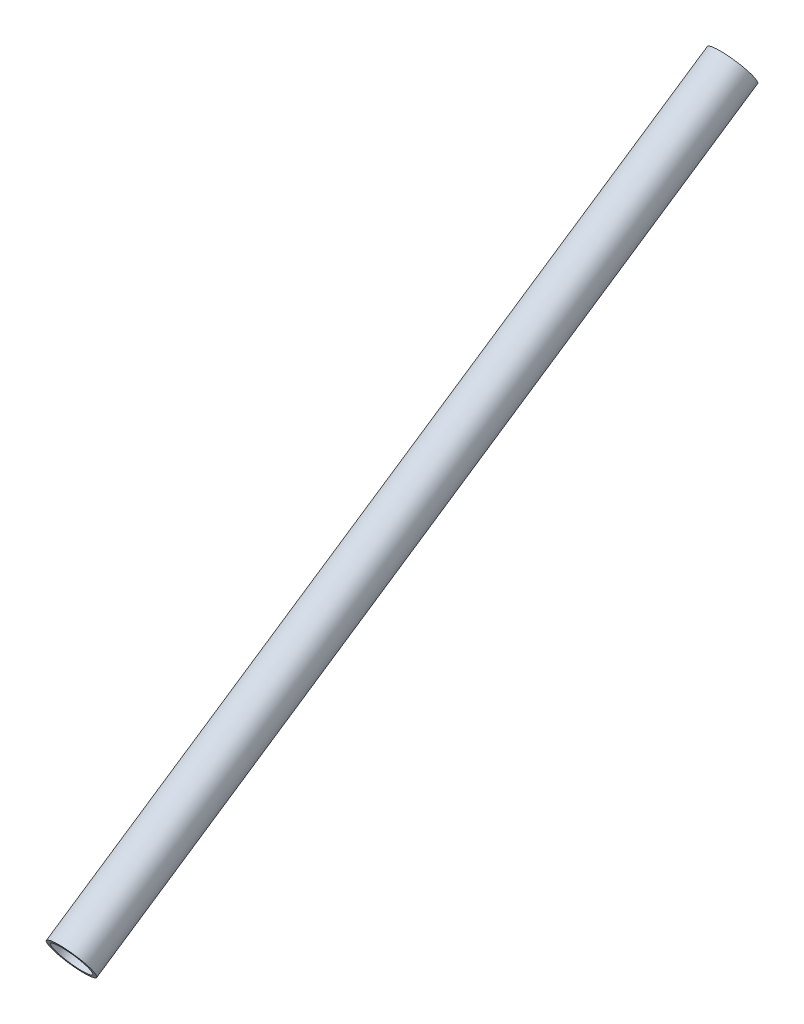
SolidWorks part; units mm, degrees
material "AISI 4130 Steel (McMaster EZ Weld Tubes)"
ref_plane "Top" through (0, 0, 0) normal (0, 0, 1) x (1, 0, 0)
ref_plane "Right" through (0, 0, 0) normal (0, 1, 0) x (1, 0, 0)
ref_plane "Front" through (0, 0, 0) normal (1, 0, 0) x (0, 0, -1)
sketch3d "3DSketch1"
  line L0 (0, 474.175, 162.9402) -> (0, 314.9632, 400.1155)
  line L1 (0, 219.6337, 542.1263) -> (0, 492.7557, 135.2608) construction
  dimension "D2" = 171.0403
  dimension "D1" = 33.3375
other "Alroundtubing 0.625 OD X 0.049 WALL(1)"
ref_plane "Plane1" through (0, 474.175, 162.9402) normal (0, -0.5574, 0.8303) x (1, 0, 0)
sketch "Sketch1" plane through (0, 474.175, 162.9402) normal (0, -0.5574, 0.8303) x (1, 0, 0)
  circle A0 centre (0, 0) radius 6.6929
  circle A1 centre (0, 0) radius 7.9375
  point P3 (0, 0)
  dimension "In_dia" = 13.3858
  dimension "Out_dia" = 15.875
equation "\"D2@3DSketch1\"= 6.433869in + 0.3"
